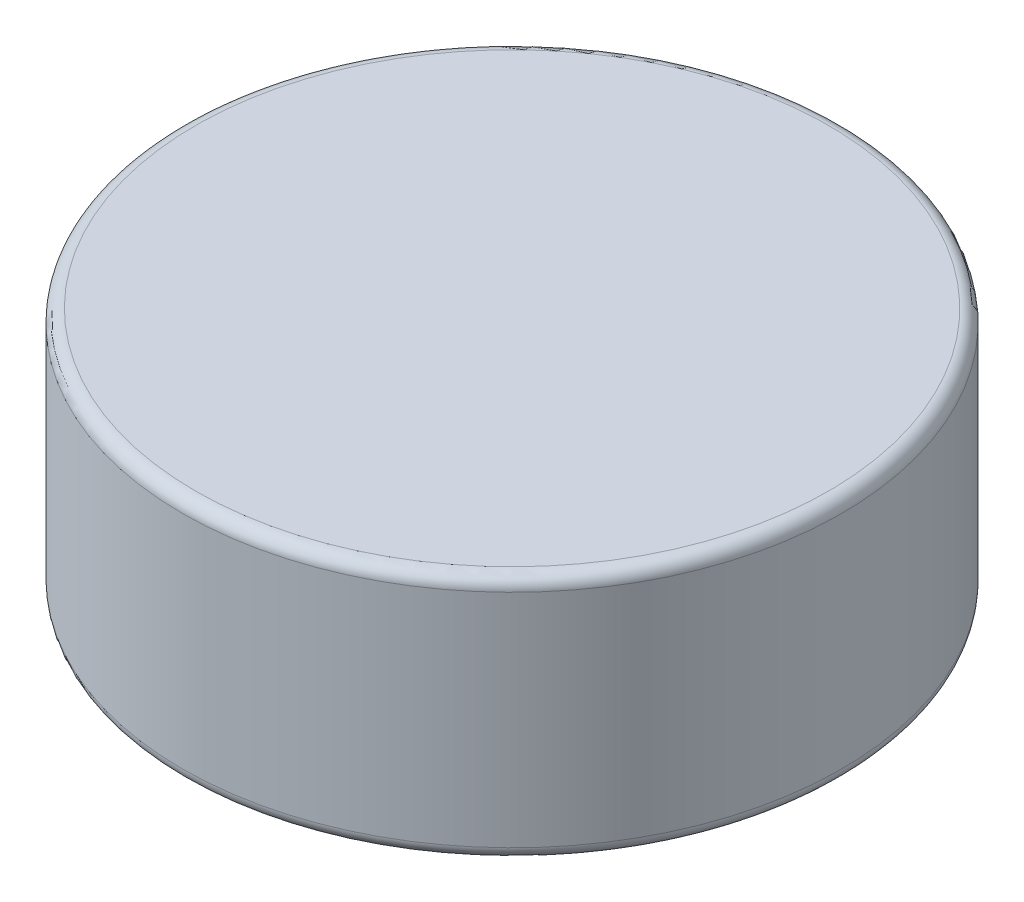
SolidWorks part; units mm, degrees
material "Neodymium"
ref_plane "Front Plane" through (0, 0, 0) normal (0, 0, 1) x (1, 0, 0)
ref_plane "Top Plane" through (0, 0, 0) normal (0, 1, 0) x (1, 0, 0)
ref_plane "Right Plane" through (0, 0, 0) normal (1, 0, 0) x (0, 0, -1)
sketch "Sketch1" plane through (0, 0, 0) normal (0, 1, 0) x (1, 0, 0)
  circle A0 centre (0, 0) radius 12.7
  dimension "D1" = 25.4
extrude "Boss-Extrude1" add sketch "Sketch1" along normal mid plane 9.525
fillet "Fillet1" radius 0.5 2 edges at (0, -4.7625, 12.7) (0, 4.7625, 12.7)
